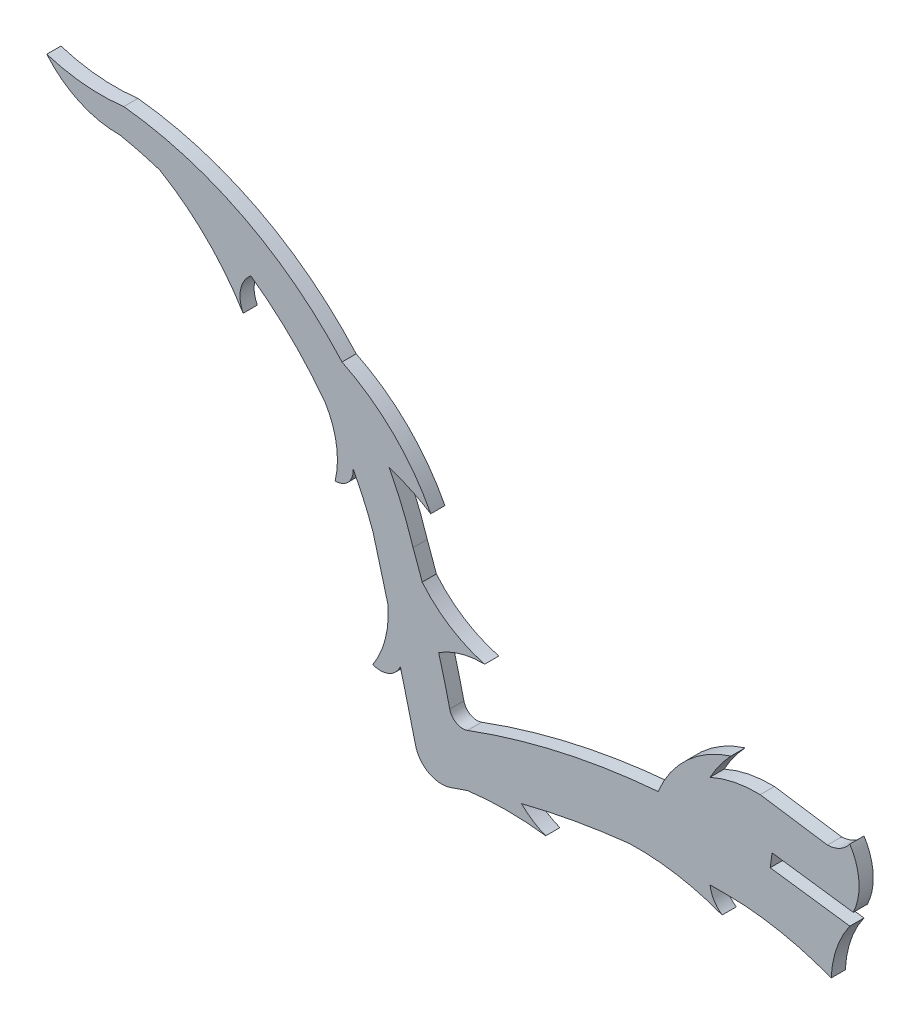
SolidWorks part; units mm, degrees
ref_plane "Front Plane" through (0, 0, 0) normal (0, 0, 1) x (1, 0, 0)
ref_plane "Top Plane" through (0, 0, 0) normal (0, 1, 0) x (1, 0, 0)
ref_plane "Right Plane" through (0, 0, 0) normal (1, 0, 0) x (0, 0, -1)
sketch "Sketch1" plane through (0, 0, 0) normal (0, 0, 1) x (1, 0, 0)
  line L230 (-229.7333, 584.7193) -> (-222.5025, 583.635)
  line L231 (-219.7211, 578.7535) -> (-228.4597, 579.935)
  line L232 (-228.4597, 579.935) -> (-228.6617, 578.4421)
  line L233 (-228.6617, 578.4421) -> (-220.0923, 577.2837)
  arc A0 (-261.2333, 569.3422) -> (-252.8134, 569.3422) centre (-257.0234, 537.1642) cw
  arc A1 (-252.8134, 569.3422) -> (-255.4236, 571.0353) centre (-250.1922, 576.242) cw
  arc A2 (-261.2333, 569.3422) -> (-263.0421, 568.7212) centre (-234.7327, 489.2205) ccw
  arc A3 (-243.8126, 573.1212) -> (-233.8343, 571.4459) centre (-243.003, 547.3897) cw
  arc A4 (-233.8343, 571.4459) -> (-235.1345, 573.6102) centre (-232.0549, 573.9876) cw
  arc A5 (-243.8126, 573.1212) -> (-255.4236, 571.0353) centre (-234.7327, 489.2205) ccw
  arc A6 (-294.3331, 610.6084) -> (-285.3755, 601.7552) centre (-307.4856, 588.3423) cw
  arc A7 (-285.3755, 601.7552) -> (-284.549, 605.6621) centre (-282.5451, 603.1973) cw
  arc A8 (-276.5708, 597.8998) -> (-275.4736, 591.0779) centre (-284.2646, 593.1632) cw
  arc A9 (-275.4736, 591.0779) -> (-273.5408, 593.1632) centre (-275.459, 593.0027) ccw
  arc A10 (-269.796, 582.3988) -> (-271.4306, 575.9857) centre (-279.9406, 581.5696) cw
  arc A11 (-271.4306, 575.9857) -> (-268.462, 577.2837) centre (-270.6189, 578.1728) ccw
  arc A12 (-269.796, 582.3988) -> (-271.4306, 588.4552) centre (-926.8783, 408.3044) ccw
  arc A13 (-276.5708, 597.8998) -> (-284.549, 605.6621) centre (-305.7339, 575.9068) ccw
  arc A14 (-294.3331, 610.6084) -> (-298.6568, 611.741) centre (-305.7339, 575.9068) ccw
  arc A15 (-231.3133, 573.5418) -> (-222.1007, 571.4459) centre (-233.772, 541.4397) cw
  arc A16 (-222.1007, 571.4459) -> (-220.0923, 577.2837) centre (-211.2335, 570.9717) cw
  arc A17 (-219.7211, 578.7535) -> (-220.0923, 584.9314) centre (-225.4792, 581.5076) ccw
  arc A18 (-220.0923, 584.9314) -> (-222.5025, 583.635) centre (-222.6216, 586.7451) cw
  arc A19 (-240.722, 579.5162) -> (-232.8783, 586.7451) centre (-229.0811, 574.7552) cw
  arc A20 (-232.8783, 586.7451) -> (-235.1345, 583.635) centre (-221.7757, 576.3173) ccw
  arc A21 (-235.1345, 583.635) -> (-229.7333, 584.7193) centre (-230.0791, 572.4478) cw
  arc A22 (-274.7363, 602.5354) -> (-265.188, 593.1632) centre (-284.1652, 583.3794) cw
  arc A23 (-265.188, 593.1632) -> (-269.6577, 595.2223) centre (-275.0771, 577.5778) ccw
  arc A24 (-274.7363, 602.5354) -> (-298.2226, 614.5977) centre (-302.1313, 578.091) ccw
  arc A25 (-266.1112, 586.3323) -> (-259.3927, 582.0426) centre (-255.9716, 594.8069) ccw
  arc A26 (-259.3927, 582.0426) -> (-264.3392, 580.6544) centre (-259.6146, 573.3262) ccw
  arc A27 (-266.1112, 586.3323) -> (-267.0921, 589.0578) centre (-363.4396, 552.8425) ccw
  arc A28 (-298.6568, 611.741) -> (-306.511, 615.335) centre (-298.8125, 621.78) cw
  arc A29 (-298.2226, 614.5977) -> (-306.511, 615.335) centre (-300.6696, 634.0461) cw
  arc A660 (-231.3133, 573.5418) -> (-235.1345, 573.6102) centre (-234.7327, 489.2205) ccw
  arc A661 (-266.8208, 570.7547) -> (-263.0421, 568.7212) centre (-264.0123, 571.4459) ccw
  arc A662 (-266.8208, 570.7547) -> (-268.462, 577.2837) centre (-926.8783, 408.3044) ccw
  arc A663 (-271.4306, 588.4552) -> (-273.5408, 593.1632) centre (-305.7339, 575.9068) ccw
  arc A665 (-267.0921, 589.0578) -> (-269.6577, 595.2223) centre (-302.1313, 578.091) ccw
  arc A666 (-263.1462, 575.9857) -> (-264.3392, 580.6544) centre (-363.4396, 552.8425) ccw
  arc A667 (-263.1462, 575.9857) -> (-261.2333, 574.9552) centre (-261.737, 576.3108) ccw
  arc A668 (-240.722, 579.5162) -> (-261.2333, 574.9552) centre (-234.4305, 502.82) ccw
extrude "Boss-Extrude1" add sketch "Sketch1" along normal blind 1.524
